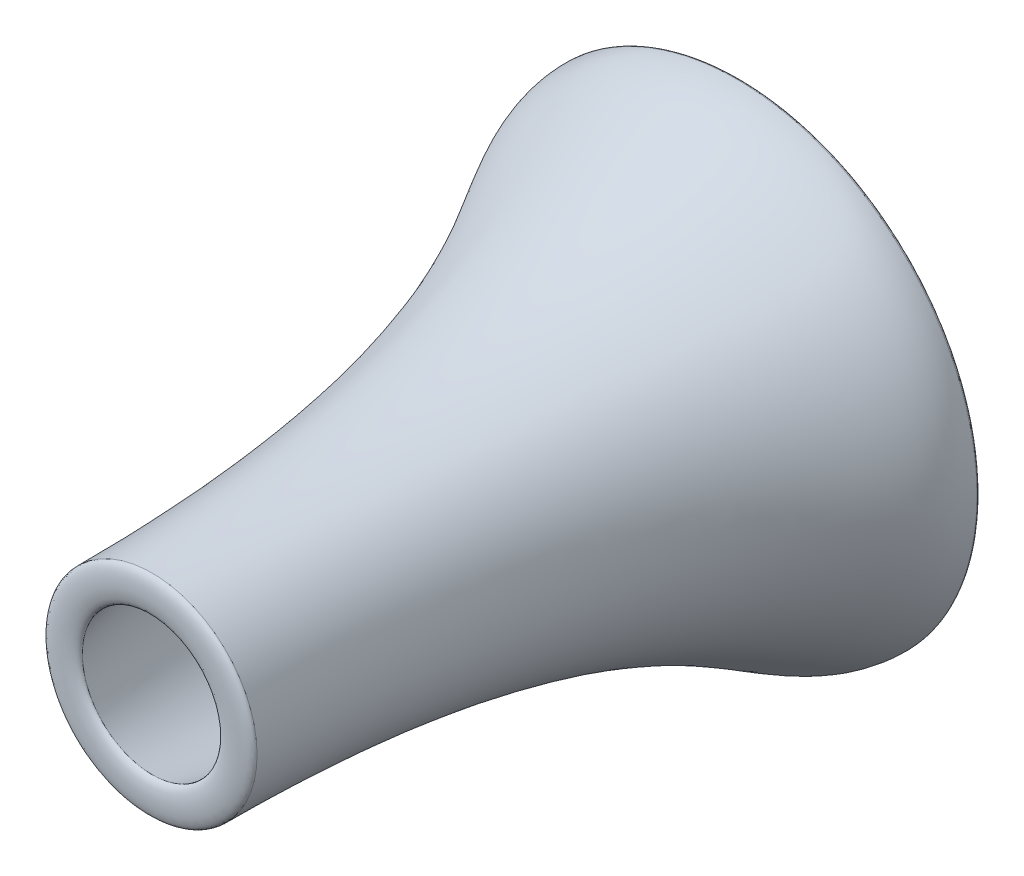
SolidWorks part; units mm, degrees
ref_plane "Front Plane" through (0, 0, 0) normal (0, 0, 1) x (1, 0, 0)
ref_plane "Top Plane" through (0, 0, 0) normal (0, 1, 0) x (1, 0, 0)
ref_plane "Right Plane" through (0, 0, 0) normal (1, 0, 0) x (0, 0, -1)
sketch "Sketch1" plane through (0, 0, 0) normal (0, 0, 1) x (1, 0, 0)
  circle A0 centre (0, 0) radius 50.8
  dimension "D1" = 101.6
ref_plane "Plane1" through (0, -254, 0) normal (0, 1, 0) x (1, 0, 0)
sketch "Sketch6" plane through (0, 0, 0) normal (0, 1, 0) x (1, 0, 0)
  line L0 (0, -99.6848) -> (0, 145.6048) construction
ref_plane "Plane2" through (0, -114.3, 0) normal (0, 1, 0) x (1, 0, 0)
sketch "Sketch12" plane through (0, 0, 0) normal (0, 1, 0) x (1, 0, 0)
  line L0 (0, -1104.7568) -> (0, -908.6135) construction
ref_plane "Plane3" through (0, 0, 203.2) normal (0, 0, 1) x (1, 0, 0)
ref_plane "Plane4" through (0, 0, 889) normal (0, 0, 1) x (1, 0, 0)
sketch "Sketch17" plane through (0, 0, 0) normal (0, 1, 0) x (1, 0, 0)
  line L0 (-259.4955, -43.5301) -> (-259.4955, 70.1436) construction
  line L1 (-110.6437, -1316.1124) -> (-110.6437, -853.5386) construction
  line L2 (-259.4955, 45.4622) -> (-387.328, 45.4622)
  line L3 (-387.328, 45.4622) -> (-387.328, -1084.8928)
  line L4 (-387.328, -1084.8928) -> (-110.6437, -1084.8928)
  spline S0 degree 3 poles (-259.4955, 45.4622) (-259.4955, -7.1736) (-207.7477, -105.8122) (-173.3147, -383.1384) (-92.4228, -818.9689) (-110.6437, -795.7842) (-110.6437, -1084.8928) knots 0 0 0 0 0.158009 0.206507 0.484977 1 1 1 1
sketch "Sketch21" plane through (0, 0, 0) normal (0, 1, 0) x (1, 0, 0)
  line L0 (-381.2499, -22.8536) -> (-381.2499, 113.778) construction
  line L1 (-166.464, -1315.9117) -> (-166.464, -853.874) construction
  line L2 (-259.4955, -167.5611) -> (-381.2499, -167.5611) construction
  line L3 (-110.6437, -1094.6547) -> (-166.464, -1094.6547) construction
  line L4 (-110.6437, -1094.6547) -> (-166.464, -1094.6547)
  line L6 (-259.4955, -167.5611) -> (-381.2499, -167.5611)
  spline S0 degree 3 poles (-259.4955, -167.5611) (-243.4812, -195.1946) (-128.674, -903.3201) (-183.485, -717.3312) (-110.6437, -1094.6547) knots 0 0 0 0 0.206507 1 1 1 1
  spline S1 degree 3 poles (-381.2499, -167.5611) (-381.2499, -292.945) (-166.464, -364.3456) (-166.464, -1094.6547) knots 0 0 0 0 1 1 1 1
  point P10 (-381.2499, 54.2551)
  point P11 (-211.14, -398.8981)
  point P12 (-110.8549, -751.1345)
  point P13 (-166.464, -1094.6547)
  point P14 (-166.464, -725.8713)
revolve "Revolve2" add sketch "Sketch21" angle 360 about L0
sketch "Sketch22" plane through (0, 0, 0) normal (0, 1, 0) x (1, 0, 0)
  line L0 (-381.2499, -167.5611) -> (-259.4955, -167.5611)
  line L1 (-259.4955, -171.3701) -> (-259.4955, -163.752) construction
  line L2 (-381.2499, -166.1683) -> (-381.2499, -168.9538) construction
  spline S0 degree 3 poles (-381.2499, -167.5611) (-381.2499, -150.6277) (-259.4955, -150.6277) (-259.4955, -167.5611) knots 0 0 0 0 1 1 1 1
revolve "Revolve3" add sketch "Sketch22" angle 360 about L0
sketch "Sketch23" plane through (0, 0, 0) normal (0, 1, 0) x (1, 0, 0)
  line L0 (-166.464, -1094.6547) -> (-110.6437, -1094.6547)
  line L1 (-166.464, -1103.8657) -> (-166.464, -1085.4436) construction
  line L2 (-110.6437, -1084.0817) -> (-110.6437, -1105.2277) construction
  spline S0 degree 3 poles (-166.464, -1094.6547) (-166.464, -1107.3547) (-110.6437, -1107.3547) (-110.6437, -1094.6547) knots 0 0 0 0 1 1 1 1
revolve "Revolve4" add sketch "Sketch23" angle 360 about L0
ref_plane "Plane5" through (289.9098, 0, 0) normal (1, 0, 0) x (0, 0, -1)
sketch "Sketch24" plane through (289.9098, 0, 0) normal (1, 0, 0) x (0, 0, -1)
  line L0 (-1123.5724, -17.6357) -> (119.2276, -17.6357) construction
  line L1 (-1094.6547, 0) -> (-167.5611, 0) construction
  line L2 (-1094.6547, -166.464) -> (-1094.6547, 166.464) construction
  line L3 (-167.5611, 381.2499) -> (-167.5611, -381.2499) construction
  text T0 "MD-130 Gas Turbine Engine" font "TI-Nspire" height in points 160
